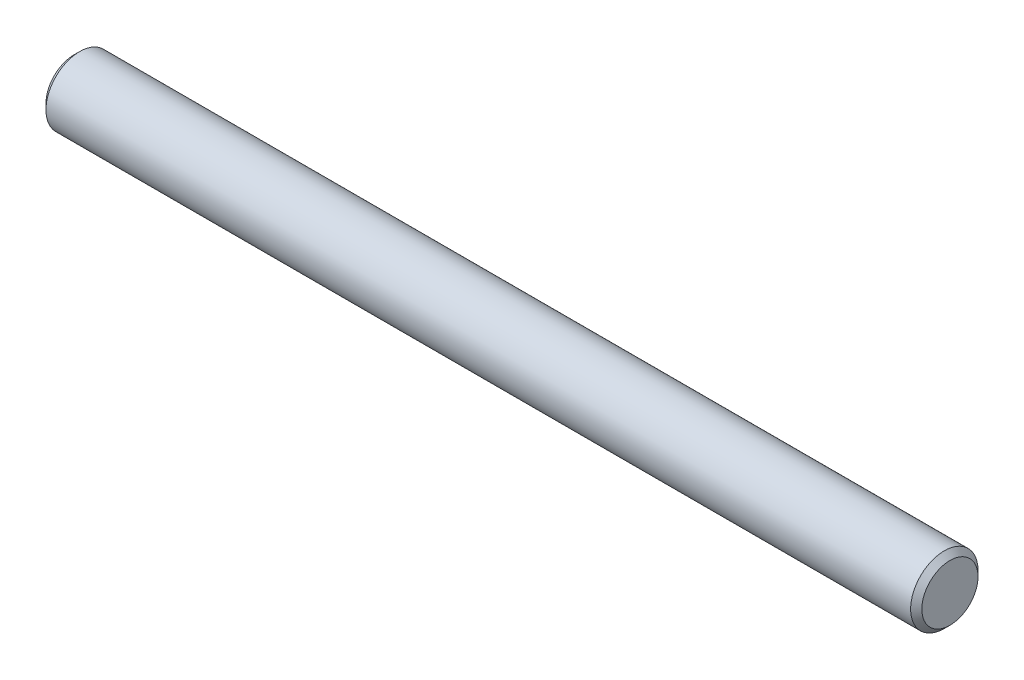
SolidWorks part; units mm, degrees
material "2014 Legierung"
ref_plane "Ebene vorne" through (0, 0, 0) normal (0, 0, 1) x (1, 0, 0)
ref_plane "Ebene oben" through (0, 0, 0) normal (0, 1, 0) x (1, 0, 0)
ref_plane "Ebene rechts" through (0, 0, 0) normal (1, 0, 0) x (0, 0, -1)
sketch "Skizze1" plane through (0, 0, 0) normal (1, 0, 0) x (0, 0, -1)
  circle A0 centre (0, 0) radius 3
  dimension "D1" = 6
extrude "Aufsatz-Linear austragen1" add sketch "Skizze1" along normal mid plane 78
chamfer "Fase1" distance 0.5 angle 45 2 edges at (-39, 0, -3) (39, 0, -3)
